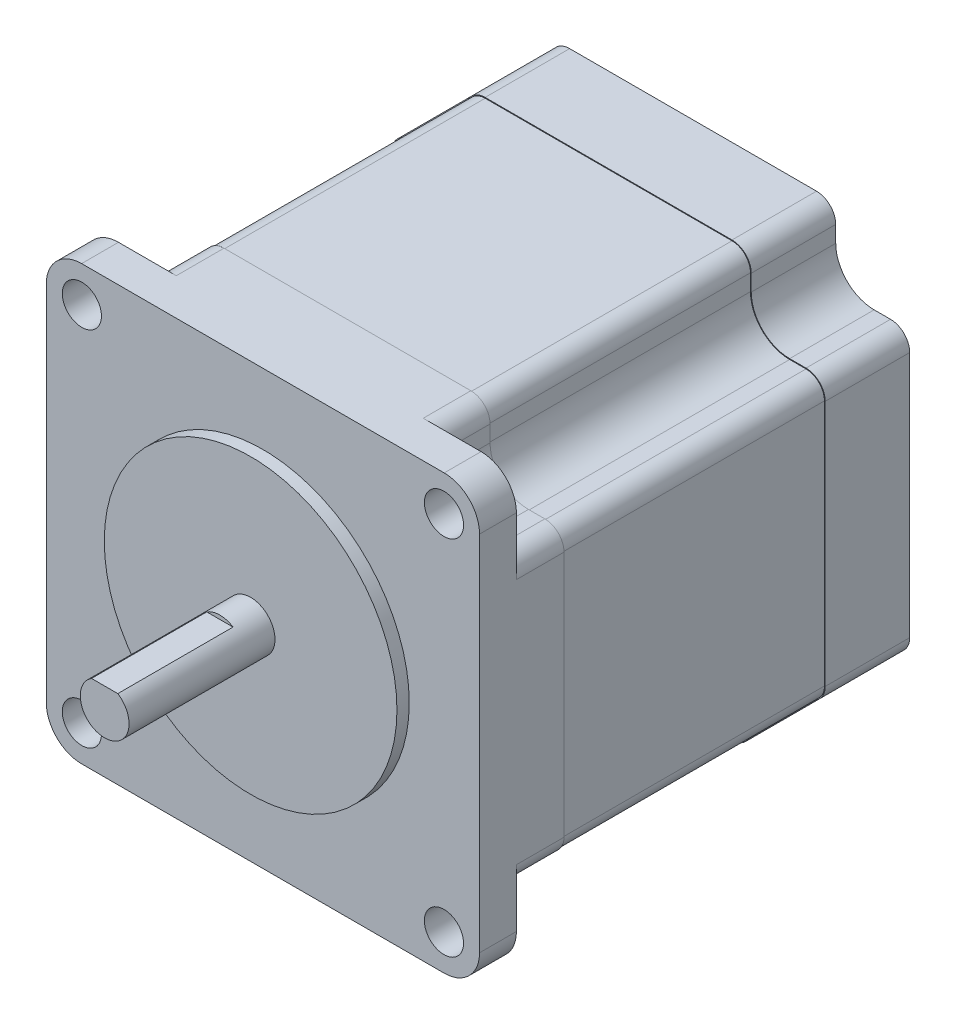
SolidWorks part; units mm, degrees
material "Plain Carbon Steel"
ref_plane "Front" through (0, 0, 0) normal (0, 0, 1) x (1, 0, 0)
ref_plane "Top" through (0, 0, 0) normal (0, 1, 0) x (1, 0, 0)
ref_plane "Right" through (0, 0, 0) normal (1, 0, 0) x (0, 0, -1)
sketch "Sketch1" plane through (0, 0, 0) normal (0, 0, 1) x (1, 0, 0)
  circle A0 centre (0, 0) radius 3.175
  dimension "D1" = 6.35
extrude "Boss-Extrude1" add sketch "Sketch1" along normal blind 20.6
sketch "Sketch2" plane through (0, 0, 0) normal (0, 0, -1) x (-1, 0, 0)
  circle A0 centre (0, 0) radius 19.05
  dimension "D1" = 38.1
extrude "Boss-Extrude2" add sketch "Sketch2" against normal blind 1.6
sketch "Sketch3" plane through (0, 0, 0) normal (0, 0, -1) x (-1, 0, 0)
  line L1 (23.6, -28.2) -> (-23.6, -28.2)
  line L2 (28.2, -23.6) -> (28.2, 23.6)
  line L3 (23.6, 28.2) -> (-23.6, 28.2)
  line L4 (-28.2, -23.6) -> (-28.2, 23.6)
  line L5 (28.2, -28.2) -> (-28.2, 28.2) construction
  line L6 (28.2, 28.2) -> (-28.2, -28.2) construction
  arc A0 (28.2, 23.6) -> (23.6, 28.2) centre (23.6, 23.6) ccw
  arc A1 (23.6, -28.2) -> (28.2, -23.6) centre (23.6, -23.6) ccw
  arc A2 (-23.6, -28.2) -> (-28.2, -23.6) centre (-23.6, -23.6) cw
  arc A3 (-23.6, 28.2) -> (-28.2, 23.6) centre (-23.6, 23.6) ccw
  point P0 (0, 0)
  dimension "D2" = 4.6
  dimension "D1" = 56.4
extrude "Boss-Extrude3" add sketch "Sketch3" along normal blind 4.8
sketch "Sketch4" plane through (0, 0, -4.8) normal (0, 0, -1) x (-1, 0, 0)
  line L0 (-12.9329, 0) -> (0, 0) construction
  line L1 (0, 0) -> (0, 12.5926) construction
  line L2 (-18.57, 23.57) -> (-18.57, 25.7)
  line L4 (28.2, 16.07) -> (28.2, -16.07)
  line L5 (-23.57, 18.57) -> (-25.7, 18.57)
  line L6 (16.07, 28.2) -> (-16.07, 28.2)
  line L7 (-28.2, 23.6) -> (-28.2, -23.6) construction
  line L8 (-28.2, 16.07) -> (-28.2, -16.07)
  line L9 (23.6, 28.2) -> (-23.6, 28.2) construction
  line L10 (23.57, 18.57) -> (25.7, 18.57)
  line L12 (18.57, 23.57) -> (18.57, 25.7)
  line L13 (18.57, -23.57) -> (18.57, -25.7)
  line L15 (23.57, -18.57) -> (25.7, -18.57)
  line L16 (16.07, -28.2) -> (-16.07, -28.2)
  line L17 (-23.57, -18.57) -> (-25.7, -18.57)
  line L19 (-18.57, -23.57) -> (-18.57, -25.7)
  arc A0 (-18.57, 25.7) -> (-16.07, 28.2) centre (-16.07, 25.7) cw
  arc A1 (-23.57, 18.57) -> (-18.57, 23.57) centre (-23.57, 23.57) ccw
  arc A2 (-25.7, 18.57) -> (-28.2, 16.07) centre (-25.7, 16.07) ccw
  arc A3 (25.7, 18.57) -> (28.2, 16.07) centre (25.7, 16.07) cw
  arc A4 (23.57, 18.57) -> (18.57, 23.57) centre (23.57, 23.57) cw
  arc A5 (18.57, 25.7) -> (16.07, 28.2) centre (16.07, 25.7) ccw
  arc A6 (18.57, -25.7) -> (16.07, -28.2) centre (16.07, -25.7) cw
  arc A7 (23.57, -18.57) -> (18.57, -23.57) centre (23.57, -23.57) ccw
  arc A8 (25.7, -18.57) -> (28.2, -16.07) centre (25.7, -16.07) ccw
  arc A9 (-25.7, -18.57) -> (-28.2, -16.07) centre (-25.7, -16.07) cw
  arc A10 (-23.57, -18.57) -> (-18.57, -23.57) centre (-23.57, -23.57) cw
  arc A11 (-18.57, -25.7) -> (-16.07, -28.2) centre (-16.07, -25.7) ccw
  point P16 (28.2, 0)
  point P27 (0, 28.2)
  point P49 (0, -28.2)
  point P51 (-28.2, 0)
  dimension "D2" = 47.14
  dimension "D3" = 2.5
  dimension "4.6*2" = 10
  dimension "D4" = 47.14
extrude "Boss-Extrude4" add sketch "Sketch4" along normal blind 51.2
sketch "Sketch7" plane through (0, 0, 20.6) normal (0, 0, 1) x (1, 0, 0)
  line L1 (-1.7103, 2.675) -> (1.7103, 2.675)
  line L2 (-1.7103, 2.675) -> (-1.7103, 3.7877)
  line L3 (-1.7103, 3.7877) -> (1.7103, 3.7877)
  line L4 (1.7103, 2.675) -> (1.7103, 3.7877)
  circle A0 centre (0, 0) radius 3.175 construction
  dimension "D1" = 5.85
extrude "Cut-Extrude5" cut sketch "Sketch7" against normal blind 15
sketch "Sketch8" plane through (0, 0, 0) normal (0, 0, 1) x (1, 0, 0)
  line L0 (-13.3219, 0) -> (0, 0) construction
  line L1 (0, 0) -> (0, 15.3153) construction
  circle A0 centre (-23.57, 23.57) radius 2.55
  circle A1 centre (23.57, 23.57) radius 2.55
  circle A2 centre (23.57, -23.57) radius 2.55
  circle A3 centre (-23.57, -23.57) radius 2.55
  dimension "D2" = 47.14
  dimension "D3" = 5.1
  dimension "D1" = 47.14
extrude "Cut-Extrude6" cut sketch "Sketch8" against normal up to next
ref_plane "Plane1" through (0, 0, -28) normal (0, 0, 1) x (1, 0, 0)
sketch "Sketch9" plane through (0, 0, -28) normal (0, 0, 1) x (1, 0, 0)
  line L24 (18.47, 23.57) -> (18.47, 25.7)
  line L25 (25.7, 18.47) -> (23.57, 18.47)
  line L26 (28.1, -16.07) -> (28.1, 16.07)
  line L27 (23.57, -18.47) -> (25.7, -18.47)
  line L28 (18.47, -25.7) -> (18.47, -23.57)
  line L29 (-16.07, -28.1) -> (16.07, -28.1)
  line L30 (-18.47, -23.57) -> (-18.47, -25.7)
  line L31 (-25.7, -18.47) -> (-23.57, -18.47)
  line L32 (-28.1, 16.07) -> (-28.1, -16.07)
  line L33 (-23.57, 18.47) -> (-25.7, 18.47)
  line L34 (-18.47, 25.7) -> (-18.47, 23.57)
  line L35 (16.07, 28.1) -> (-16.07, 28.1)
  line L36 (18.47, 23.57) -> (18.47, 25.7)
  line L37 (25.7, 18.47) -> (23.57, 18.47)
  line L38 (28.1, -16.07) -> (28.1, 16.07)
  line L39 (23.57, -18.47) -> (25.7, -18.47)
  line L40 (18.47, -25.7) -> (18.47, -23.57)
  line L41 (-16.07, -28.1) -> (16.07, -28.1)
  line L42 (-18.47, -23.57) -> (-18.47, -25.7)
  line L43 (-25.7, -18.47) -> (-23.57, -18.47)
  line L44 (-28.1, 16.07) -> (-28.1, -16.07)
  line L45 (-23.57, 18.47) -> (-25.7, 18.47)
  line L46 (-18.47, 25.7) -> (-18.47, 23.57)
  line L47 (16.07, 28.1) -> (-16.07, 28.1)
  line L48 (18.57, 23.57) -> (18.57, 25.7)
  line L49 (25.7, 18.57) -> (23.57, 18.57)
  line L50 (28.2, -16.07) -> (28.2, 16.07)
  line L51 (23.57, -18.57) -> (25.7, -18.57)
  line L52 (18.57, -25.7) -> (18.57, -23.57)
  line L53 (-16.07, -28.2) -> (16.07, -28.2)
  line L54 (-18.57, -23.57) -> (-18.57, -25.7)
  line L55 (-25.7, -18.57) -> (-23.57, -18.57)
  line L56 (-28.2, 16.07) -> (-28.2, -16.07)
  line L57 (-23.57, 18.57) -> (-25.7, 18.57)
  line L58 (-18.57, 25.7) -> (-18.57, 23.57)
  line L59 (16.07, 28.2) -> (-16.07, 28.2)
  line L60 (18.57, 23.57) -> (18.57, 25.7)
  line L61 (25.7, 18.57) -> (23.57, 18.57)
  line L62 (28.2, -16.07) -> (28.2, 16.07)
  line L63 (23.57, -18.57) -> (25.7, -18.57)
  line L64 (18.57, -25.7) -> (18.57, -23.57)
  line L65 (-16.07, -28.2) -> (16.07, -28.2)
  line L66 (-18.57, -23.57) -> (-18.57, -25.7)
  line L67 (-25.7, -18.57) -> (-23.57, -18.57)
  line L68 (-28.2, 16.07) -> (-28.2, -16.07)
  line L69 (-23.57, 18.57) -> (-25.7, 18.57)
  line L70 (-18.57, 25.7) -> (-18.57, 23.57)
  line L71 (16.07, 28.2) -> (-16.07, 28.2)
  arc A24 (18.47, 25.7) -> (16.07, 28.1) centre (16.07, 25.7) ccw
  arc A25 (18.47, 23.57) -> (23.57, 18.47) centre (23.57, 23.57) ccw
  arc A26 (28.1, 16.07) -> (25.7, 18.47) centre (25.7, 16.07) ccw
  arc A27 (25.7, -18.47) -> (28.1, -16.07) centre (25.7, -16.07) ccw
  arc A28 (23.57, -18.47) -> (18.47, -23.57) centre (23.57, -23.57) ccw
  arc A29 (16.07, -28.1) -> (18.47, -25.7) centre (16.07, -25.7) ccw
  arc A30 (-18.47, -25.7) -> (-16.07, -28.1) centre (-16.07, -25.7) ccw
  arc A31 (-18.47, -23.57) -> (-23.57, -18.47) centre (-23.57, -23.57) ccw
  arc A32 (-28.1, -16.07) -> (-25.7, -18.47) centre (-25.7, -16.07) ccw
  arc A33 (-25.7, 18.47) -> (-28.1, 16.07) centre (-25.7, 16.07) ccw
  arc A34 (-23.57, 18.47) -> (-18.47, 23.57) centre (-23.57, 23.57) ccw
  arc A35 (-16.07, 28.1) -> (-18.47, 25.7) centre (-16.07, 25.7) ccw
  arc A36 (18.47, 25.7) -> (16.07, 28.1) centre (16.07, 25.7) ccw
  arc A37 (18.47, 23.57) -> (23.57, 18.47) centre (23.57, 23.57) ccw
  arc A38 (28.1, 16.07) -> (25.7, 18.47) centre (25.7, 16.07) ccw
  arc A39 (25.7, -18.47) -> (28.1, -16.07) centre (25.7, -16.07) ccw
  arc A40 (23.57, -18.47) -> (18.47, -23.57) centre (23.57, -23.57) ccw
  arc A41 (16.07, -28.1) -> (18.47, -25.7) centre (16.07, -25.7) ccw
  arc A42 (-18.47, -25.7) -> (-16.07, -28.1) centre (-16.07, -25.7) ccw
  arc A43 (-18.47, -23.57) -> (-23.57, -18.47) centre (-23.57, -23.57) ccw
  arc A44 (-28.1, -16.07) -> (-25.7, -18.47) centre (-25.7, -16.07) ccw
  arc A45 (-25.7, 18.47) -> (-28.1, 16.07) centre (-25.7, 16.07) ccw
  arc A46 (-23.57, 18.47) -> (-18.47, 23.57) centre (-23.57, 23.57) ccw
  arc A47 (-16.07, 28.1) -> (-18.47, 25.7) centre (-16.07, 25.7) ccw
  arc A48 (18.57, 25.7) -> (16.07, 28.2) centre (16.07, 25.7) ccw
  arc A49 (18.57, 23.57) -> (23.57, 18.57) centre (23.57, 23.57) ccw
  arc A50 (28.2, 16.07) -> (25.7, 18.57) centre (25.7, 16.07) ccw
  arc A51 (25.7, -18.57) -> (28.2, -16.07) centre (25.7, -16.07) ccw
  arc A52 (23.57, -18.57) -> (18.57, -23.57) centre (23.57, -23.57) ccw
  arc A53 (16.07, -28.2) -> (18.57, -25.7) centre (16.07, -25.7) ccw
  arc A54 (-18.57, -25.7) -> (-16.07, -28.2) centre (-16.07, -25.7) ccw
  arc A55 (-18.57, -23.57) -> (-23.57, -18.57) centre (-23.57, -23.57) ccw
  arc A56 (-28.2, -16.07) -> (-25.7, -18.57) centre (-25.7, -16.07) ccw
  arc A57 (-25.7, 18.57) -> (-28.2, 16.07) centre (-25.7, 16.07) ccw
  arc A58 (-23.57, 18.57) -> (-18.57, 23.57) centre (-23.57, 23.57) ccw
  arc A59 (-16.07, 28.2) -> (-18.57, 25.7) centre (-16.07, 25.7) ccw
  arc A60 (18.57, 25.7) -> (16.07, 28.2) centre (16.07, 25.7) ccw
  arc A61 (18.57, 23.57) -> (23.57, 18.57) centre (23.57, 23.57) ccw
  arc A62 (28.2, 16.07) -> (25.7, 18.57) centre (25.7, 16.07) ccw
  arc A63 (25.7, -18.57) -> (28.2, -16.07) centre (25.7, -16.07) ccw
  arc A64 (23.57, -18.57) -> (18.57, -23.57) centre (23.57, -23.57) ccw
  arc A65 (16.07, -28.2) -> (18.57, -25.7) centre (16.07, -25.7) ccw
  arc A66 (-18.57, -25.7) -> (-16.07, -28.2) centre (-16.07, -25.7) ccw
  arc A67 (-18.57, -23.57) -> (-23.57, -18.57) centre (-23.57, -23.57) ccw
  arc A68 (-28.2, -16.07) -> (-25.7, -18.57) centre (-25.7, -16.07) ccw
  arc A69 (-25.7, 18.57) -> (-28.2, 16.07) centre (-25.7, 16.07) ccw
  arc A70 (-23.57, 18.57) -> (-18.57, 23.57) centre (-23.57, 23.57) ccw
  arc A71 (-16.07, 28.2) -> (-18.57, 25.7) centre (-16.07, 25.7) ccw
  dimension "D1" = 0.1
  dimension "D2" = 0
extrude "Cut-Extrude7" cut sketch "Sketch9" against normal mid plane 34
